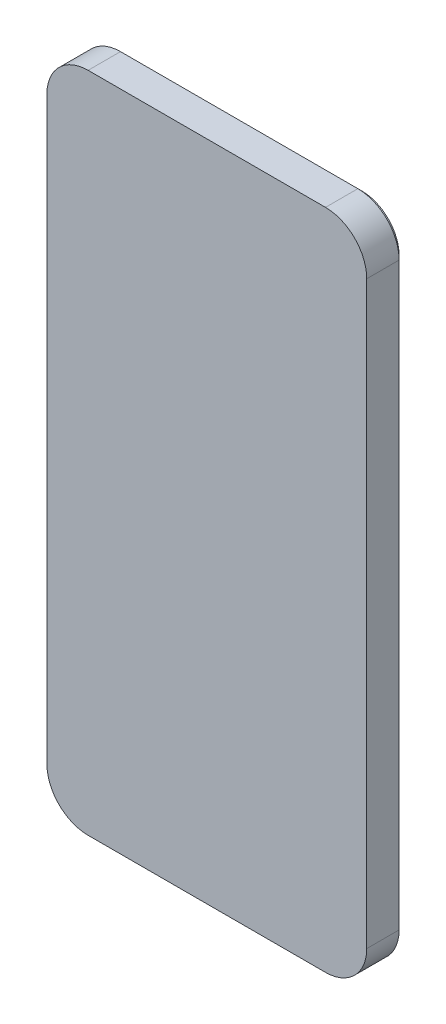
SolidWorks part; units mm, degrees
ref_plane "Ön Düzlem" through (0, 0, 0) normal (0, 0, 1) x (1, 0, 0)
ref_plane "Üst Düzlem" through (0, 0, 0) normal (0, 1, 0) x (1, 0, 0)
ref_plane "Sağ Düzlem" through (0, 0, 0) normal (1, 0, 0) x (0, 0, -1)
sketch "Çizim1" plane through (0, 0, 0) normal (0, 0, 1) x (1, 0, 0)
  line L1 (-22.8455, 30.2356) -> (54.7345, 30.2356)
  line L2 (-22.8455, 30.2356) -> (-22.8455, -130.4644)
  line L3 (-22.8455, -130.4644) -> (54.7345, -130.4644)
  line L4 (54.7345, 30.2356) -> (54.7345, -130.4644)
  dimension "D1" = 77.58
  dimension "D2" = 160.7
extrude "Yükseklik-Ekstrüzyon1" add sketch "Çizim1" along normal blind 7.85
fillet "Radyus1" radius 10 4 edges at (54.7345, -130.4644, 3.925) (-22.8455, -130.4644, 3.925) (-22.8455, 30.2356, 3.925) (54.7345, 30.2356, 3.925)
sketch "Çizim3" plane through (0, 0, 0) normal (0, 0, -1) x (-1, 0, 0)
  line L0 (-42.7345, 28.2356) -> (-22.7345, 28.2356)
  line L1 (-52.7345, 18.2356) -> (-52.7345, -1.7644)
  line L2 (-42.7345, -11.7644) -> (-22.7345, -11.7644)
  line L3 (-12.7345, 18.2356) -> (-12.7345, -1.7644)
  arc A0 (-42.7345, 28.2356) -> (-52.7345, 18.2356) centre (-42.7345, 18.2356) ccw
  arc A1 (-12.7345, 18.2356) -> (-22.7345, 28.2356) centre (-22.7345, 18.2356) ccw
  arc A2 (-22.7345, -11.7644) -> (-12.7345, -1.7644) centre (-22.7345, -1.7644) ccw
  arc A3 (-52.7345, -1.7644) -> (-42.7345, -11.7644) centre (-42.7345, -1.7644) ccw
  dimension "D1" = 2
  dimension "D2" = 2
extrude "Yükseklik-Ekstrüzyon2" add sketch "Çizim3" along normal blind 2
sketch "Çizim7" plane through (0, 0, -2) normal (0, 0, -1) x (-1, 0, 0)
  line L4 (-42.7345, 27.2356) -> (-22.7345, 27.2356)
  line L5 (-13.7345, 18.2356) -> (-13.7345, -1.7644)
  line L6 (-42.7345, -10.7644) -> (-22.7345, -10.7644)
  line L7 (-51.7345, 18.2356) -> (-51.7345, -1.7644)
  arc A4 (-13.7345, 18.2356) -> (-22.7345, 27.2356) centre (-22.7345, 18.2356) ccw
  arc A5 (-22.7345, -10.7644) -> (-13.7345, -1.7644) centre (-22.7345, -1.7644) ccw
  arc A6 (-51.7345, -1.7644) -> (-42.7345, -10.7644) centre (-42.7345, -1.7644) ccw
  arc A7 (-42.7345, 27.2356) -> (-51.7345, 18.2356) centre (-42.7345, 18.2356) ccw
extrude "Yükseklik-Ekstrüzyon3" add sketch "Çizim7" along normal blind 1
fillet "Radyus3" radius 0.8 8 edges at (15.6634, 25.3066, -2) (12.7345, 8.2356, -2) (15.6634, -8.8355, -2) (32.7345, -11.7644, -2) (49.8056, -8.8355, -2) (52.7345, 8.2356, -2) (49.8056, 25.3066, -2) (32.7345, 28.2356, -2)
